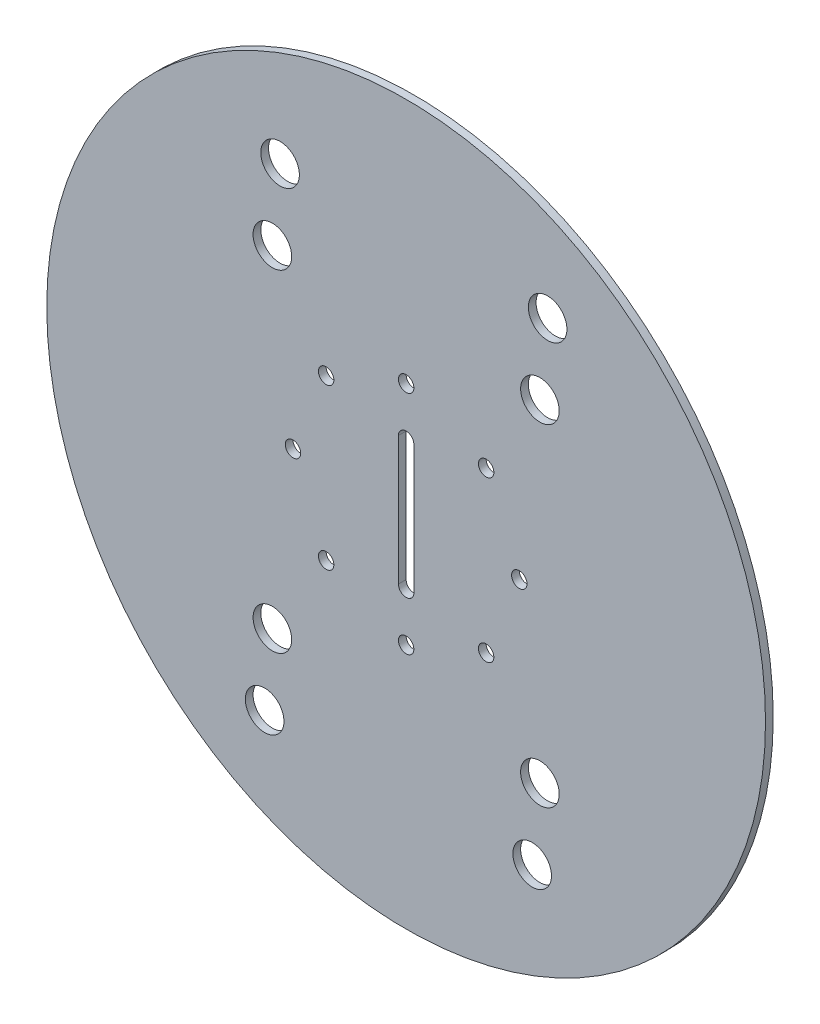
SolidWorks part; units mm, degrees
material "Teak"
ref_plane "Front Plane" through (0, 0, 0) normal (0, 0, 1) x (1, 0, 0)
ref_plane "Top Plane" through (0, 0, 0) normal (0, 1, 0) x (1, 0, 0)
ref_plane "Right Plane" through (0, 0, 0) normal (1, 0, 0) x (0, 0, -1)
sketch "Sketch1" plane through (0, 0, 0) normal (0, 0, 1) x (1, 0, 0)
  line L0 (0, 139.7) -> (0, -139.7) construction
  line L1 (-139.7, 0) -> (139.7, 0) construction
  circle A0 centre (0, 0) radius 139.7
  dimension "D1" = 279.4
extrude "Boss-Extrude1" add sketch "Sketch1" along normal blind 3
sketch "Sketch2" plane through (0, 0, 3) normal (0, 0, 1) x (1, 0, 0)
  line L0 (-55.2472, 0) -> (0, 52.4804) construction
  line L1 (-139.7, 0) -> (139.7, 0) construction
  line L2 (0, 139.7) -> (0, -139.7) construction
  line L3 (-3, -25) -> (-3, 25)
  line L4 (0, 28.3292) -> (0, 0) construction
  line L5 (0, 0) -> (-3, 0) construction
  line L6 (3, -25) -> (3, 25)
  circle A0 centre (0, 43.9804) radius 3
  circle A1 centre (31.0988, 31.0988) radius 3
  circle A2 centre (43.9804, 0) radius 3
  circle A3 centre (31.0988, -31.0988) radius 3
  arc A4 (-3, 25) -> (3, 25) centre (0, 25) cw
  arc A5 (-3, -25) -> (3, -25) centre (0, -25) ccw
  circle A6 centre (0, -43.9804) radius 3
  circle A7 centre (-31.0988, -31.0988) radius 3
  circle A8 centre (-43.9804, 0) radius 3
  circle A9 centre (-31.0988, 31.0988) radius 3
  point P17 (0, 0)
  point P25 (3, 0)
  dimension "D2" = 6
  dimension "D1" = 76.2
  dimension "D3" = 8.5
  dimension "D5" = 6
  dimension "D6" = 50
  dimension "D4" = 8
extrude "Cut-Extrude1" cut sketch "Sketch2" against normal through all
sketch "Sketch3" plane through (0, 0, 3) normal (0, 0, 1) x (1, 0, 0)
  line L0 (-139.7, 0) -> (139.7, 0) construction
  line L1 (0, 139.7) -> (0, -139.7) construction
  line L2 (-73.0748, 0) -> (73.0748, 0) construction
  line L3 (0, 85.0253) -> (0, -85.0253) construction
  circle A0 centre (-52, -64.5) radius 7.5
  circle A1 centre (-55, -93.5) radius 7.5
  circle A2 centre (52, 64.5) radius 7.5
  circle A3 centre (55, 93.5) radius 7.5
  circle A4 centre (52, -64.5) radius 7.5
  circle A5 centre (49, -93.5) radius 7.5
  circle A6 centre (-52, 64.5) radius 7.5
  circle A7 centre (-49, 93.5) radius 7.5
  point P18 (0, 0)
  point P20 (0, 0)
  point P30 (0, 0)
  dimension "D3" = 15
  dimension "D1" = 64.5
  dimension "D2" = 52
  dimension "D5" = 29
  dimension "D6" = 3
  dimension "D8" = 3
  dimension "D9" = 29
  dimension "D4" = 2
  dimension "D7" = 2
  dimension "D10" = 2
extrude "Cut-Extrude2" cut sketch "Sketch3" against normal through all
equation "\"D9@Sketch3\"=\"D5@Sketch3\""
